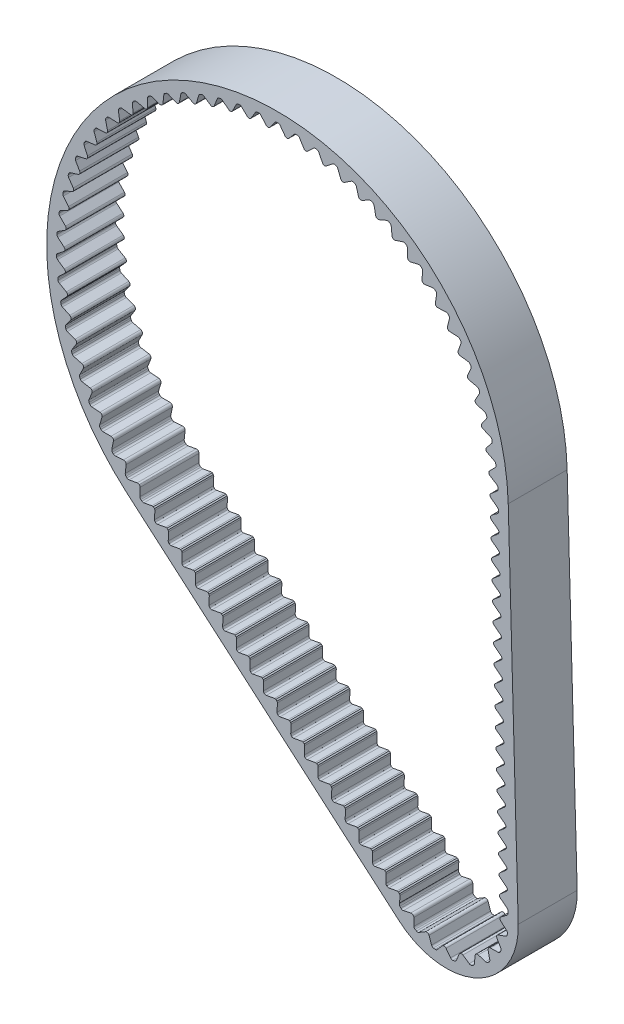
SolidWorks part; units mm, degrees
ref_plane "Face" through (0, 0, 0) normal (0, 0, 1) x (1, 0, 0)
ref_plane "Dessus" through (0, 0, 0) normal (0, 1, 0) x (1, 0, 0)
ref_plane "Droite" through (0, 0, 0) normal (1, 0, 0) x (0, 0, -1)
ref_plane "Plan1" through (0, 0, 6) normal (0, 0, 1) x (1, 0, 0)
sketch "Esquisse1" plane through (0, 0, 6) normal (0, 0, 1) x (1, 0, 0)
  line L0 (-15.3344, -17.8075) -> (12.3909, -41.6822)
  line L1 (24.5093, -35.9199) -> (23.4909, 0.6541)
  line L2 (22.6969, -34.5303) -> (23.3588, -35.04)
  line L3 (23.4562, -35.2422) -> (23.4441, -35.2419)
  line L4 (23.3776, -35.6789) -> (22.7552, -36.1447)
  line L5 (22.7403, -36.5329) -> (23.325, -37.0452)
  line L6 (23.2117, -37.6167) -> (22.4758, -37.8674)
  line L7 (22.3416, -38.2319) -> (22.7394, -38.8999)
  line L8 (22.4551, -39.4084) -> (21.6778, -39.4194)
  line L9 (21.4375, -39.7247) -> (21.6094, -40.4829)
  line L10 (21.1819, -40.8787) -> (20.4392, -40.6489)
  line L11 (20.1163, -40.865) -> (20.0455, -41.6392)
  line L12 (19.5166, -41.8835) -> (18.8812, -41.4354)
  line L13 (18.5074, -41.5412) -> (18.2008, -42.2556)
  line L14 (17.6223, -42.3245) -> (17.1565, -41.7021)
  line L15 (16.7683, -41.6871) -> (16.256, -42.2718)
  line L16 (15.6845, -42.1586) -> (15.4338, -41.4227)
  line L17 (15.0692, -41.2885) -> (14.4013, -41.6863)
  line L18 (13.8928, -41.402) -> (13.8818, -40.6246)
  line L19 (13.5765, -40.3843) -> (12.8183, -40.5562)
  line L20 (12.5335, -40.4331) -> (12.5299, -40.4377)
  line L21 (12.4225, -40.1287) -> (12.4389, -40.0758)
  line L22 (12.4389, -40.0758) -> (12.4571, -39.3994)
  line L23 (12.4207, -39.2626) -> (12.3042, -39.1623)
  line L24 (12.162, -39.1468) -> (11.3403, -39.2978)
  line L25 (11.1249, -39.2349) -> (11.1282, -39.2307)
  line L26 (11.0487, -39.0411) -> (11.0711, -38.2059)
  line L27 (11.0348, -38.0691) -> (10.9183, -37.9688)
  line L28 (10.776, -37.9533) -> (9.9543, -38.1043)
  line L29 (9.7389, -38.0415) -> (9.7422, -38.0372)
  line L30 (9.6627, -37.8476) -> (9.6851, -37.0124)
  line L31 (9.6488, -36.8757) -> (9.5323, -36.7754)
  line L32 (9.3901, -36.7599) -> (8.5684, -36.9108)
  line L33 (8.353, -36.848) -> (8.3563, -36.8437)
  line L34 (8.2768, -36.6541) -> (8.2992, -35.819)
  line L35 (8.2629, -35.6822) -> (8.1464, -35.5819)
  line L36 (8.0041, -35.5664) -> (7.1824, -35.7173)
  line L37 (6.967, -35.6545) -> (6.9703, -35.6503)
  line L38 (6.8908, -35.4607) -> (6.9132, -34.6255)
  line L39 (6.8769, -34.4887) -> (6.7604, -34.3884)
  line L40 (6.6182, -34.3729) -> (5.7965, -34.5239)
  line L41 (5.581, -34.4611) -> (5.5844, -34.4568)
  line L42 (5.5049, -34.2672) -> (5.5273, -33.432)
  line L43 (5.4909, -33.2953) -> (5.3745, -33.195)
  line L44 (5.2322, -33.1794) -> (4.4105, -33.3304)
  line L45 (4.1951, -33.2676) -> (4.1984, -33.2633)
  line L46 (4.1189, -33.0737) -> (4.1413, -32.2386)
  line L47 (4.105, -32.1018) -> (3.9885, -32.0015)
  line L48 (3.8462, -31.986) -> (3.0245, -32.1369)
  line L49 (2.8091, -32.0741) -> (2.8125, -32.0698)
  line L50 (2.733, -31.8802) -> (2.7554, -31.0451)
  line L51 (2.719, -30.9083) -> (2.6026, -30.808)
  line L52 (2.4603, -30.7925) -> (1.6386, -30.9435)
  line L53 (1.4232, -30.8807) -> (1.4265, -30.8764)
  line L54 (1.347, -30.6868) -> (1.3694, -29.8516)
  line L55 (1.3331, -29.7148) -> (1.2166, -29.6145)
  line L56 (1.0743, -29.599) -> (0.2526, -29.75)
  line L57 (0.0372, -29.6872) -> (0.0405, -29.6829)
  line L58 (-0.0389, -29.4933) -> (-0.0165, -28.6582)
  line L59 (-0.0529, -28.5214) -> (-0.1693, -28.4211)
  line L60 (-0.3116, -28.4056) -> (-1.1333, -28.5565)
  line L61 (-1.3487, -28.4937) -> (-1.3454, -28.4894)
  line L62 (-1.4249, -28.2998) -> (-1.4025, -27.4647)
  line L63 (-1.4388, -27.3279) -> (-1.5553, -27.2276)
  line L64 (-1.6976, -27.2121) -> (-2.5193, -27.363)
  line L65 (-2.7347, -27.3002) -> (-2.7314, -27.296)
  line L66 (-2.8108, -27.1064) -> (-2.7884, -26.2712)
  line L67 (-2.8248, -26.1344) -> (-2.9413, -26.0341)
  line L68 (-3.0835, -26.0186) -> (-3.9052, -26.1696)
  line L69 (-4.1206, -26.1068) -> (-4.1173, -26.1025)
  line L70 (-4.1968, -25.9129) -> (-4.1744, -25.0777)
  line L71 (-4.2107, -24.941) -> (-4.3272, -24.8407)
  line L72 (-4.4695, -24.8252) -> (-5.2912, -24.9761)
  line L73 (-5.5066, -24.9133) -> (-5.5033, -24.909)
  line L74 (-5.5827, -24.7194) -> (-5.5603, -23.8843)
  line L75 (-5.5967, -23.7475) -> (-5.7132, -23.6472)
  line L76 (-5.8554, -23.6317) -> (-6.6771, -23.7826)
  line L77 (-6.8925, -23.7198) -> (-6.8892, -23.7155)
  line L78 (-6.9687, -23.5259) -> (-6.9463, -22.6908)
  line L79 (-6.9826, -22.554) -> (-7.0991, -22.4537)
  line L80 (-7.2414, -22.4382) -> (-8.0631, -22.5892)
  line L81 (-8.2785, -22.5264) -> (-8.2752, -22.5221)
  line L82 (-8.3547, -22.3325) -> (-8.3323, -21.4973)
  line L83 (-8.3686, -21.3606) -> (-8.4851, -21.2602)
  line L84 (-8.6273, -21.2447) -> (-9.449, -21.3957)
  line L85 (-9.6644, -21.3329) -> (-9.6611, -21.3286)
  line L86 (-9.7406, -21.139) -> (-9.7182, -20.3039)
  line L87 (-9.7545, -20.1671) -> (-9.871, -20.0668)
  line L88 (-10.0133, -20.0513) -> (-10.835, -20.2022)
  line L89 (-11.0504, -20.1394) -> (-11.0471, -20.1351)
  line L90 (-11.1266, -19.9455) -> (-11.1042, -19.1104)
  line L91 (-11.1405, -18.9736) -> (-11.257, -18.8733)
  line L92 (-11.3992, -18.8578) -> (-12.2209, -19.0087)
  line L93 (-12.4364, -18.9459) -> (-12.433, -18.9417)
  line L94 (-12.5125, -18.7521) -> (-12.4901, -17.9169)
  line L95 (-12.5265, -17.7801) -> (-12.6429, -17.6798)
  line L96 (-12.7852, -17.6643) -> (-13.6069, -17.8153)
  line L97 (-14.0119, -17.4767) -> (-13.9895, -16.6416)
  line L98 (-14.0711, -16.45) -> (-14.0815, -16.441)
  line L99 (-14.2846, -16.389) -> (-15.1063, -16.54)
  line L100 (-15.5016, -16.17) -> (-15.4055, -15.3401)
  line L101 (-15.6771, -15.0624) -> (-16.5089, -15.1401)
  line L102 (-16.8701, -14.7367) -> (-16.701, -13.9185)
  line L103 (-16.947, -13.6179) -> (-17.7824, -13.6218)
  line L104 (-18.1065, -13.188) -> (-17.8658, -12.388)
  line L105 (-18.0842, -12.0668) -> (-18.9167, -11.9969)
  line L106 (-19.2012, -11.5362) -> (-18.8907, -10.7606)
  line L107 (-19.0799, -10.4213) -> (-19.903, -10.2781)
  line L108 (-20.1456, -9.794) -> (-19.7678, -9.0489)
  line L109 (-19.9263, -8.6943) -> (-20.7335, -8.4789)
  line L110 (-20.9324, -7.9752) -> (-20.4902, -7.2664)
  line L111 (-20.6167, -6.8992) -> (-21.4017, -6.6132)
  line L112 (-21.5553, -6.094) -> (-21.0522, -5.427)
  line L113 (-21.1458, -5.0501) -> (-21.9025, -4.6959)
  line L114 (-22.0096, -4.1651) -> (-21.4495, -3.5452)
  line L115 (-21.5094, -3.1614) -> (-22.2318, -2.7418)
  line L116 (-22.2916, -2.2036) -> (-21.6789, -1.6356)
  line L117 (-21.7046, -1.248) -> (-22.3871, -0.7662)
  line L118 (-22.3991, -0.2248) -> (-21.7386, 0.2868)
  line L119 (-21.73, 0.6751) -> (-22.3672, 1.2154)
  line L120 (-22.3313, 1.7557) -> (-21.6282, 2.2069)
  line L121 (-21.5853, 2.5929) -> (-22.1723, 3.1874)
  line L122 (-22.0887, 3.7225) -> (-21.3485, 4.1098)
  line L123 (-21.2717, 4.4905) -> (-21.8038, 5.1346)
  line L124 (-21.6733, 5.6601) -> (-20.9017, 5.9805)
  line L125 (-20.7915, 6.3529) -> (-21.2647, 7.0415)
  line L126 (-21.0883, 7.5534) -> (-20.2914, 7.8044)
  line L127 (-20.1487, 8.1656) -> (-20.5591, 8.8933)
  line L128 (-20.3382, 9.3877) -> (-19.5222, 9.5672)
  line L129 (-19.3482, 9.9144) -> (-19.6927, 10.6755)
  line L130 (-19.4289, 11.1484) -> (-18.6003, 11.2551)
  line L131 (-18.3962, 11.5856) -> (-18.6721, 12.3742)
  line L132 (-18.3676, 12.8219) -> (-17.5328, 12.855)
  line L133 (-17.3003, 13.1661) -> (-17.5054, 13.976)
  line L134 (-17.1625, 14.3951) -> (-16.328, 14.3542)
  line L135 (-16.069, 14.6436) -> (-16.2017, 15.4685)
  line L136 (-15.8231, 15.8556) -> (-14.9955, 15.7411)
  line L137 (-14.7119, 16.0065) -> (-14.7712, 16.8398)
  line L138 (-14.3599, 17.192) -> (-13.5456, 17.0048)
  line L139 (-13.2397, 17.2441) -> (-13.2251, 18.0794)
  line L140 (-12.7842, 18.3938) -> (-11.9897, 18.1354)
  line L141 (-11.6638, 18.3467) -> (-11.5755, 19.1775)
  line L142 (-11.1086, 19.4517) -> (-10.34, 19.1241)
  line L143 (-9.9967, 19.3058) -> (-9.8353, 20.1255)
  line L144 (-9.3459, 20.3574) -> (-8.6094, 19.9631)
  line L145 (-8.2513, 20.1138) -> (-8.0181, 20.916)
  line L146 (-7.5102, 21.1037) -> (-6.8113, 20.6459)
  line L147 (-6.4414, 20.7643) -> (-6.1382, 21.5428)
  line L148 (-5.6157, 21.6849) -> (-4.96, 21.1671)
  line L149 (-4.581, 21.2523) -> (-4.2102, 22.001)
  line L150 (-3.6772, 22.0963) -> (-3.0698, 21.5226)
  line L151 (-2.6848, 21.5741) -> (-2.2493, 22.287)
  line L152 (-1.7099, 22.3348) -> (-1.1556, 21.7097)
  line L153 (-0.7676, 21.7269) -> (-0.2707, 22.3986)
  line L154 (0.2707, 22.3986) -> (0.7676, 21.7269)
  line L155 (1.1556, 21.7097) -> (1.7099, 22.3348)
  line L156 (2.2493, 22.287) -> (2.6848, 21.5741)
  line L157 (3.0698, 21.5226) -> (3.6772, 22.0963)
  line L158 (4.2102, 22.001) -> (4.581, 21.2523)
  line L159 (4.96, 21.1671) -> (5.6157, 21.6849)
  line L160 (6.1382, 21.5428) -> (6.4414, 20.7643)
  line L161 (6.8113, 20.6459) -> (7.5102, 21.1037)
  line L162 (8.0181, 20.916) -> (8.2513, 20.1138)
  line L163 (8.6094, 19.9631) -> (9.3459, 20.3574)
  line L164 (9.8353, 20.1255) -> (9.9967, 19.3058)
  line L165 (10.34, 19.1241) -> (11.1086, 19.4517)
  line L166 (11.5755, 19.1775) -> (11.6638, 18.3467)
  line L167 (11.9897, 18.1354) -> (12.7842, 18.3938)
  line L168 (13.2251, 18.0794) -> (13.2397, 17.2441)
  line L169 (13.5456, 17.0048) -> (14.3599, 17.192)
  line L170 (14.7712, 16.8398) -> (14.7119, 16.0065)
  line L171 (14.9955, 15.7411) -> (15.8231, 15.8556)
  line L172 (16.2017, 15.4685) -> (16.069, 14.6436)
  line L173 (16.328, 14.3542) -> (17.1625, 14.3951)
  line L174 (17.5054, 13.976) -> (17.3003, 13.1661)
  line L175 (17.5328, 12.855) -> (18.3676, 12.8219)
  line L176 (18.6721, 12.3742) -> (18.3962, 11.5856)
  line L177 (18.6003, 11.2551) -> (19.4289, 11.1484)
  line L178 (19.6927, 10.6755) -> (19.3482, 9.9144)
  line L179 (19.5222, 9.5672) -> (20.3382, 9.3877)
  line L180 (20.5591, 8.8933) -> (20.1487, 8.1656)
  line L181 (20.2914, 7.8044) -> (21.0883, 7.5534)
  line L182 (21.2647, 7.0415) -> (20.7915, 6.3529)
  line L183 (20.9017, 5.9805) -> (21.6733, 5.6601)
  line L184 (21.8038, 5.1346) -> (21.2717, 4.4905)
  line L185 (21.3485, 4.1098) -> (22.0887, 3.7225)
  line L186 (22.1723, 3.1874) -> (21.5853, 2.5929)
  line L187 (21.6282, 2.2069) -> (22.3313, 1.7557)
  line L188 (22.3672, 1.2154) -> (21.73, 0.6751)
  line L189 (21.6417, 0.4908) -> (21.6425, 0.4641)
  line L190 (21.7386, 0.2868) -> (22.3991, -0.2248)
  line L191 (22.3871, -0.7662) -> (21.9854, -1.0498)
  line L192 (21.9854, -1.0498) -> (21.7709, -1.2327)
  line L193 (21.6931, -1.3529) -> (21.6974, -1.5065)
  line L194 (21.7805, -1.621) -> (22.4424, -2.1308)
  line L195 (22.5393, -2.3121) -> (22.5447, -2.3123)
  line L196 (22.4575, -2.519) -> (22.337, -2.6217)
  line L197 (22.2318, -2.7418) -> (22.1202, -2.8066)
  line L198 (22.1202, -2.8066) -> (21.8218, -3.061)
  line L199 (21.744, -3.1812) -> (21.7483, -3.3348)
  line L200 (21.8314, -3.4493) -> (22.4933, -3.9591)
  line L201 (22.5902, -4.1404) -> (22.5956, -4.1405)
  line L202 (22.5084, -4.3473) -> (21.8727, -4.8893)
  line L203 (21.7949, -5.0095) -> (21.7992, -5.1631)
  line L204 (21.8823, -5.2776) -> (22.5442, -5.7874)
  line L205 (22.6411, -5.9687) -> (22.6466, -5.9688)
  line L206 (22.5593, -6.1756) -> (21.9236, -6.7176)
  line L207 (21.8458, -6.8378) -> (21.8501, -6.9914)
  line L208 (21.9332, -7.1059) -> (22.5952, -7.6157)
  line L209 (22.6921, -7.797) -> (22.6975, -7.7971)
  line L210 (22.6102, -8.0038) -> (21.9745, -8.5459)
  line L211 (21.8967, -8.666) -> (21.901, -8.8197)
  line L212 (21.9842, -8.9342) -> (22.6461, -9.444)
  line L213 (22.743, -9.6253) -> (22.7484, -9.6254)
  line L214 (22.6611, -9.8321) -> (22.0254, -10.3742)
  line L215 (21.9476, -10.4943) -> (21.9519, -10.648)
  line L216 (22.0351, -10.7625) -> (22.697, -11.2723)
  line L217 (22.7939, -11.4536) -> (22.7993, -11.4537)
  line L218 (22.712, -11.6604) -> (22.0763, -12.2025)
  line L219 (21.9985, -12.3226) -> (22.0028, -12.4763)
  line L220 (22.086, -12.5908) -> (22.7479, -13.1005)
  line L221 (22.8448, -13.2819) -> (22.8502, -13.282)
  line L222 (22.7629, -13.4887) -> (22.1272, -14.0308)
  line L223 (22.0495, -14.1509) -> (22.0537, -14.3046)
  line L224 (22.1369, -14.4191) -> (22.7988, -14.9288)
  line L225 (22.8957, -15.1102) -> (22.9011, -15.1103)
  line L226 (22.8139, -15.317) -> (22.1781, -15.8591)
  line L227 (22.1004, -15.9792) -> (22.1046, -16.1329)
  line L228 (22.1878, -16.2474) -> (22.8497, -16.7571)
  line L229 (22.9466, -16.9385) -> (22.952, -16.9386)
  line L230 (22.8648, -17.1453) -> (22.229, -17.6874)
  line L231 (22.1513, -17.8075) -> (22.1556, -17.9612)
  line L232 (22.2387, -18.0757) -> (22.9006, -18.5854)
  line L233 (22.9975, -18.7667) -> (23.0029, -18.7669)
  line L234 (22.9157, -18.9736) -> (22.28, -19.5157)
  line L235 (22.2022, -19.6358) -> (22.2065, -19.7894)
  line L236 (22.2896, -19.904) -> (22.9515, -20.4137)
  line L237 (23.0484, -20.595) -> (23.0538, -20.5952)
  line L238 (22.9666, -20.8019) -> (22.3309, -21.3439)
  line L239 (22.2531, -21.4641) -> (22.2574, -21.6177)
  line L240 (22.3405, -21.7323) -> (23.0024, -22.242)
  line L241 (23.0993, -22.4233) -> (23.1047, -22.4235)
  line L242 (23.0175, -22.6302) -> (22.3818, -23.1722)
  line L243 (22.304, -23.2924) -> (22.3083, -23.446)
  line L244 (22.3914, -23.5605) -> (23.0533, -24.0703)
  line L245 (23.1502, -24.2516) -> (23.1557, -24.2517)
  line L246 (23.0684, -24.4585) -> (22.4327, -25.0005)
  line L247 (22.3549, -25.1207) -> (22.3592, -25.2743)
  line L248 (22.4423, -25.3888) -> (23.1043, -25.8986)
  line L249 (23.2012, -26.0799) -> (23.2066, -26.08)
  line L250 (23.1193, -26.2868) -> (22.4836, -26.8288)
  line L251 (22.4058, -26.949) -> (22.4101, -27.1026)
  line L252 (22.4933, -27.2171) -> (23.1552, -27.7269)
  line L253 (23.2521, -27.9082) -> (23.2575, -27.9083)
  line L254 (23.1702, -28.1151) -> (22.5345, -28.6571)
  line L255 (22.4567, -28.7773) -> (22.461, -28.9309)
  line L256 (22.5442, -29.0454) -> (23.2061, -29.5552)
  line L257 (23.303, -29.7365) -> (23.3084, -29.7366)
  line L258 (23.2211, -29.9433) -> (22.5854, -30.4854)
  line L259 (22.5076, -30.6055) -> (22.5119, -30.7592)
  line L260 (22.5951, -30.8737) -> (23.257, -31.3835)
  line L261 (23.3539, -31.5648) -> (23.3593, -31.5649)
  line L262 (23.272, -31.7716) -> (22.6363, -32.3137)
  line L263 (22.5586, -32.4338) -> (22.5628, -32.5875)
  line L264 (22.646, -32.702) -> (23.3079, -33.2118)
  line L265 (23.4048, -33.3931) -> (23.4102, -33.3932)
  line L266 (23.323, -33.5999) -> (22.6872, -34.142)
  line L267 (22.6802, -34.1482) -> (22.6193, -34.2346)
  line L268 (22.6095, -34.2621) -> (22.6137, -34.4158)
  line L269 (0, 0) -> (17.1772, -36.124) construction
  line L270 (0, -52.5) -> (0, 52.5) construction
  arc A0 (12.3909, -41.6822) -> (24.5093, -35.9199) centre (17.1772, -36.124) ccw
  arc A1 (23.4909, 0.6541) -> (-15.3344, -17.8075) centre (0, 0) ccw
  arc A2 (23.3588, -35.04) -> (23.4562, -35.2422) centre (23.2063, -35.2381) cw
  arc A3 (23.4441, -35.2419) -> (23.458, -35.2975) centre (23.2101, -35.3301) cw
  arc A4 (23.458, -35.2975) -> (23.4764, -35.4522) centre (17.1772, -36.124) cw
  arc A5 (23.4764, -35.4522) -> (23.3776, -35.6789) centre (23.2278, -35.4787) cw
  arc A6 (22.7552, -36.1447) -> (22.7403, -36.5329) centre (22.905, -36.3448) ccw
  arc A7 (23.325, -37.0452) -> (23.406, -37.2788) centre (23.1602, -37.2332) cw
  arc A8 (23.406, -37.2788) -> (23.3757, -37.4317) centre (17.1772, -36.124) cw
  arc A9 (23.3757, -37.4317) -> (23.2117, -37.6167) centre (23.1311, -37.3801) cw
  arc A10 (22.4758, -37.8674) -> (22.3416, -38.2319) centre (22.5564, -38.104) ccw
  arc A11 (22.7394, -38.8999) -> (22.7443, -39.1471) centre (22.5246, -39.0278) cw
  arc A12 (22.7443, -39.1471) -> (22.6683, -39.2831) centre (17.1772, -36.124) cw
  arc A13 (22.6683, -39.2831) -> (22.4551, -39.4084) centre (22.4516, -39.1585) cw
  arc A14 (21.6778, -39.4194) -> (21.4375, -39.7247) centre (21.6813, -39.6694) ccw
  arc A15 (21.6094, -40.4829) -> (21.5377, -40.7195) centre (21.3656, -40.5381) cw
  arc A16 (21.5377, -40.7195) -> (21.4233, -40.8254) centre (17.1772, -36.124) cw
  arc A17 (21.4233, -40.8254) -> (21.1819, -40.8787) centre (21.2557, -40.6398) cw
  arc A18 (20.4392, -40.6489) -> (20.1163, -40.865) centre (20.3653, -40.8877) ccw
  arc A19 (20.0455, -41.6392) -> (19.9042, -41.842) centre (19.7965, -41.6164) cw
  arc A20 (19.9042, -41.842) -> (19.7627, -41.9074) centre (17.1772, -36.124) cw
  arc A21 (19.7627, -41.9074) -> (19.5166, -41.8835) centre (19.6607, -41.6792) cw
  arc A22 (18.8812, -41.4354) -> (18.5074, -41.5412) centre (18.7372, -41.6398) ccw
  arc A23 (18.2008, -42.2556) -> (18.0037, -42.4049) centre (17.9711, -42.157) cw
  arc A24 (18.0037, -42.4049) -> (17.849, -42.4233) centre (17.1772, -36.124) cw
  arc A25 (17.849, -42.4233) -> (17.6223, -42.3245) centre (17.8225, -42.1747) cw
  arc A26 (17.1565, -41.7021) -> (16.7683, -41.6871) centre (16.9564, -41.8519) ccw
  arc A27 (16.256, -42.2718) -> (16.0224, -42.3529) centre (16.068, -42.1071) cw
  arc A28 (16.0224, -42.3529) -> (15.8695, -42.3226) centre (17.1772, -36.124) cw
  arc A29 (15.8695, -42.3226) -> (15.6845, -42.1586) centre (15.9211, -42.078) cw
  arc A30 (15.4338, -41.4227) -> (15.0692, -41.2885) centre (15.1972, -41.5033) ccw
  arc A31 (14.4013, -41.6863) -> (14.1541, -41.6912) centre (14.2734, -41.4715) cw
  arc A32 (14.1541, -41.6912) -> (14.0181, -41.6151) centre (17.1772, -36.124) cw
  arc A33 (14.0181, -41.6151) -> (13.8928, -41.402) centre (14.1427, -41.3984) cw
  arc A34 (13.8818, -40.6246) -> (13.5765, -40.3843) centre (13.6318, -40.6282) ccw
  arc A35 (12.8183, -40.5562) -> (12.5817, -40.4845) centre (12.763, -40.3124) cw
  arc A36 (12.5817, -40.4845) -> (12.5335, -40.4331) centre (17.1772, -36.124) cw
  arc A37 (12.5299, -40.4377) -> (12.4595, -40.3501) centre (12.6846, -40.2412) cw
  arc A38 (12.4595, -40.3501) -> (12.4225, -40.1287) centre (12.6614, -40.2026) cw
  arc A39 (12.4571, -39.3994) -> (12.4207, -39.2626) centre (12.2071, -39.3926) ccw
  arc A40 (12.3042, -39.1623) -> (12.162, -39.1468) centre (12.2071, -39.3927) ccw
  arc A41 (11.3403, -39.2978) -> (11.1249, -39.2349) centre (11.2951, -39.0519) cw
  arc A42 (11.1282, -39.2307) -> (11.0487, -39.0411) centre (11.2986, -39.0478) cw
  arc A43 (11.0711, -38.2059) -> (11.0348, -38.0691) centre (10.8212, -38.1991) ccw
  arc A44 (10.9183, -37.9688) -> (10.776, -37.9533) centre (10.8212, -38.1992) ccw
  arc A45 (9.9543, -38.1043) -> (9.7389, -38.0415) centre (9.9091, -37.8584) cw
  arc A46 (9.7422, -38.0372) -> (9.6627, -37.8476) centre (9.9127, -37.8543) cw
  arc A47 (9.6851, -37.0124) -> (9.6488, -36.8757) centre (9.4352, -37.0056) ccw
  arc A48 (9.5323, -36.7754) -> (9.3901, -36.7599) centre (9.4352, -37.0057) ccw
  arc A49 (8.5684, -36.9108) -> (8.353, -36.848) centre (8.5232, -36.6649) cw
  arc A50 (8.3563, -36.8437) -> (8.2768, -36.6541) centre (8.5267, -36.6608) cw
  arc A51 (8.2992, -35.819) -> (8.2629, -35.6822) centre (8.0493, -35.8122) ccw
  arc A52 (8.1464, -35.5819) -> (8.0041, -35.5664) centre (8.0493, -35.8123) ccw
  arc A53 (7.1824, -35.7173) -> (6.967, -35.6545) centre (7.1372, -35.4715) cw
  arc A54 (6.9703, -35.6503) -> (6.8908, -35.4607) centre (7.1407, -35.4674) cw
  arc A55 (6.9132, -34.6255) -> (6.8769, -34.4887) centre (6.6633, -34.6187) ccw
  arc A56 (6.7604, -34.3884) -> (6.6182, -34.3729) centre (6.6633, -34.6188) ccw
  arc A57 (5.7965, -34.5239) -> (5.581, -34.4611) centre (5.7513, -34.278) cw
  arc A58 (5.5844, -34.4568) -> (5.5049, -34.2672) centre (5.7548, -34.2739) cw
  arc A59 (5.5273, -33.432) -> (5.4909, -33.2953) centre (5.2774, -33.4252) ccw
  arc A60 (5.3745, -33.195) -> (5.2322, -33.1794) centre (5.2774, -33.4253) ccw
  arc A61 (4.4105, -33.3304) -> (4.1951, -33.2676) centre (4.3653, -33.0845) cw
  arc A62 (4.1984, -33.2633) -> (4.1189, -33.0737) centre (4.3688, -33.0804) cw
  arc A63 (4.1413, -32.2386) -> (4.105, -32.1018) centre (3.8914, -32.2317) ccw
  arc A64 (3.9885, -32.0015) -> (3.8462, -31.986) centre (3.8914, -32.2319) ccw
  arc A65 (3.0245, -32.1369) -> (2.8091, -32.0741) centre (2.9794, -31.891) cw
  arc A66 (2.8125, -32.0698) -> (2.733, -31.8802) centre (2.9829, -31.8869) cw
  arc A67 (2.7554, -31.0451) -> (2.719, -30.9083) centre (2.5055, -31.0383) ccw
  arc A68 (2.6026, -30.808) -> (2.4603, -30.7925) centre (2.5055, -31.0384) ccw
  arc A69 (1.6386, -30.9435) -> (1.4232, -30.8807) centre (1.5934, -30.6976) cw
  arc A70 (1.4265, -30.8764) -> (1.347, -30.6868) centre (1.5969, -30.6935) cw
  arc A71 (1.3694, -29.8516) -> (1.3331, -29.7148) centre (1.1195, -29.8448) ccw
  arc A72 (1.2166, -29.6145) -> (1.0743, -29.599) centre (1.1195, -29.8449) ccw
  arc A73 (0.2526, -29.75) -> (0.0372, -29.6872) centre (0.2075, -29.5041) cw
  arc A74 (0.0405, -29.6829) -> (-0.0389, -29.4933) centre (0.211, -29.5) cw
  arc A75 (-0.0165, -28.6582) -> (-0.0529, -28.5214) centre (-0.2664, -28.6513) ccw
  arc A76 (-0.1693, -28.4211) -> (-0.3116, -28.4056) centre (-0.2664, -28.6514) ccw
  arc A77 (-1.1333, -28.5565) -> (-1.3487, -28.4937) centre (-1.1785, -28.3106) cw
  arc A78 (-1.3454, -28.4894) -> (-1.4249, -28.2998) centre (-1.175, -28.3065) cw
  arc A79 (-1.4025, -27.4647) -> (-1.4388, -27.3279) centre (-1.6524, -27.4579) ccw
  arc A80 (-1.5553, -27.2276) -> (-1.6976, -27.2121) centre (-1.6524, -27.458) ccw
  arc A81 (-2.5193, -27.363) -> (-2.7347, -27.3002) centre (-2.5644, -27.1172) cw
  arc A82 (-2.7314, -27.296) -> (-2.8108, -27.1064) centre (-2.5609, -27.1131) cw
  arc A83 (-2.7884, -26.2712) -> (-2.8248, -26.1344) centre (-3.0383, -26.2644) ccw
  arc A84 (-2.9413, -26.0341) -> (-3.0835, -26.0186) centre (-3.0384, -26.2645) ccw
  arc A85 (-3.9052, -26.1696) -> (-4.1206, -26.1068) centre (-3.9504, -25.9237) cw
  arc A86 (-4.1173, -26.1025) -> (-4.1968, -25.9129) centre (-3.9469, -25.9196) cw
  arc A87 (-4.1744, -25.0777) -> (-4.2107, -24.941) centre (-4.4243, -25.0709) ccw
  arc A88 (-4.3272, -24.8407) -> (-4.4695, -24.8252) centre (-4.4243, -25.071) ccw
  arc A89 (-5.2912, -24.9761) -> (-5.5066, -24.9133) centre (-5.3363, -24.7302) cw
  arc A90 (-5.5033, -24.909) -> (-5.5827, -24.7194) centre (-5.3328, -24.7261) cw
  arc A91 (-5.5603, -23.8843) -> (-5.5967, -23.7475) centre (-5.8103, -23.8774) ccw
  arc A92 (-5.7132, -23.6472) -> (-5.8554, -23.6317) centre (-5.8103, -23.8776) ccw
  arc A93 (-6.6771, -23.7826) -> (-6.8925, -23.7198) centre (-6.7223, -23.5367) cw
  arc A94 (-6.8892, -23.7155) -> (-6.9687, -23.5259) centre (-6.7188, -23.5326) cw
  arc A95 (-6.9463, -22.6908) -> (-6.9826, -22.554) centre (-7.1962, -22.684) ccw
  arc A96 (-7.0991, -22.4537) -> (-7.2414, -22.4382) centre (-7.1962, -22.6841) ccw
  arc A97 (-8.0631, -22.5892) -> (-8.2785, -22.5264) centre (-8.1083, -22.3433) cw
  arc A98 (-8.2752, -22.5221) -> (-8.3547, -22.3325) centre (-8.1047, -22.3392) cw
  arc A99 (-8.3323, -21.4973) -> (-8.3686, -21.3606) centre (-8.5822, -21.4905) ccw
  arc A100 (-8.4851, -21.2602) -> (-8.6273, -21.2447) centre (-8.5822, -21.4906) ccw
  arc A101 (-9.449, -21.3957) -> (-9.6644, -21.3329) centre (-9.4942, -21.1498) cw
  arc A102 (-9.6611, -21.3286) -> (-9.7406, -21.139) centre (-9.4907, -21.1457) cw
  arc A103 (-9.7182, -20.3039) -> (-9.7545, -20.1671) centre (-9.9681, -20.297) ccw
  arc A104 (-9.871, -20.0668) -> (-10.0133, -20.0513) centre (-9.9681, -20.2972) ccw
  arc A105 (-10.835, -20.2022) -> (-11.0504, -20.1394) centre (-10.8802, -19.9563) cw
  arc A106 (-11.0471, -20.1351) -> (-11.1266, -19.9455) centre (-10.8767, -19.9522) cw
  arc A107 (-11.1042, -19.1104) -> (-11.1405, -18.9736) centre (-11.3541, -19.1036) ccw
  arc A108 (-11.257, -18.8733) -> (-11.3992, -18.8578) centre (-11.3541, -19.1037) ccw
  arc A109 (-12.2209, -19.0087) -> (-12.4364, -18.9459) centre (-12.2661, -18.7629) cw
  arc A110 (-12.433, -18.9417) -> (-12.5125, -18.7521) centre (-12.2626, -18.7588) cw
  arc A111 (-12.4901, -17.9169) -> (-12.5265, -17.7801) centre (-12.74, -17.9101) ccw
  arc A112 (-12.6429, -17.6798) -> (-12.7852, -17.6643) centre (-12.74, -17.9102) ccw
  arc A113 (-13.6069, -17.8153) -> (-13.8055, -17.7668) centre (-13.6521, -17.5694) cw
  arc A114 (-13.8055, -17.7668) -> (-13.9166, -17.6799) centre (0, 0) cw
  arc A115 (-13.9166, -17.6799) -> (-14.0119, -17.4767) centre (-13.762, -17.4834) cw
  arc A116 (-13.9895, -16.6416) -> (-14.0711, -16.45) centre (-14.2394, -16.6349) ccw
  arc A117 (-14.0815, -16.441) -> (-14.2846, -16.389) centre (-14.2394, -16.6349) ccw
  arc A118 (-15.1063, -16.54) -> (-15.3217, -16.4771) centre (-15.1514, -16.2941) cw
  arc A119 (-15.3217, -16.4771) -> (-15.4247, -16.3807) centre (0, 0) cw
  arc A120 (-15.4247, -16.3807) -> (-15.5016, -16.17) centre (-15.2533, -16.1987) cw
  arc A121 (-15.4055, -15.3401) -> (-15.6771, -15.0624) centre (-15.6539, -15.3113) ccw
  arc A122 (-16.5089, -15.1401) -> (-16.718, -15.0585) centre (-16.5322, -14.8912) cw
  arc A123 (-16.718, -15.0585) -> (-16.8121, -14.9534) centre (0, 0) cw
  arc A124 (-16.8121, -14.9534) -> (-16.8701, -14.7367) centre (-16.6253, -14.7873) cw
  arc A125 (-16.701, -13.9185) -> (-16.947, -13.6179) centre (-16.9458, -13.8679) ccw
  arc A126 (-17.7824, -13.6218) -> (-17.9834, -13.5221) centre (-17.7836, -13.3718) cw
  arc A127 (-17.9834, -13.5221) -> (-18.0679, -13.409) centre (0, 0) cw
  arc A128 (-18.0679, -13.409) -> (-18.1065, -13.188) centre (-17.8671, -13.2601) cw
  arc A129 (-17.8658, -12.388) -> (-18.0842, -12.0668) centre (-18.1052, -12.316) ccw
  arc A130 (-18.9167, -11.9969) -> (-19.1081, -11.8798) centre (-18.8958, -11.7478) cw
  arc A131 (-19.1081, -11.8798) -> (-19.1822, -11.7597) centre (0, 0) cw
  arc A132 (-19.1822, -11.7597) -> (-19.2012, -11.5362) centre (-18.9691, -11.6291) cw
  arc A133 (-18.8907, -10.7606) -> (-19.0799, -10.4213) centre (-19.1228, -10.6676) ccw
  arc A134 (-19.903, -10.2781) -> (-20.0833, -10.1445) centre (-19.8601, -10.0318) cw
  arc A135 (-20.0833, -10.1445) -> (-20.1465, -10.0184) centre (0, 0) cw
  arc A136 (-20.1465, -10.0184) -> (-20.1456, -9.794) centre (-19.9227, -9.9071) cw
  arc A137 (-19.7678, -9.0489) -> (-19.9263, -8.6943) centre (-19.9908, -8.9358) ccw
  arc A138 (-20.7335, -8.4789) -> (-20.9013, -8.3299) centre (-20.669, -8.2373) cw
  arc A139 (-20.9013, -8.3299) -> (-20.9531, -8.1986) centre (0, 0) cw
  arc A140 (-20.9531, -8.1986) -> (-20.9324, -7.9752) centre (-20.7203, -8.1075) cw
  arc A141 (-20.4902, -7.2664) -> (-20.6167, -6.8992) centre (-20.7023, -7.1341) ccw
  arc A142 (-21.4017, -6.6132) -> (-21.5557, -6.45) centre (-21.3162, -6.3783) cw
  arc A143 (-21.5557, -6.45) -> (-21.5957, -6.3147) centre (0, 0) cw
  arc A144 (-21.5957, -6.3147) -> (-21.5553, -6.094) centre (-21.3558, -6.2445) cw
  arc A145 (-21.0522, -5.427) -> (-21.1458, -5.0501) centre (-21.2518, -5.2765) ccw
  arc A146 (-21.9025, -4.6959) -> (-22.0414, -4.5197) centre (-21.7965, -4.4695) cw
  arc A147 (-22.0414, -4.5197) -> (-22.0693, -4.3814) centre (0, 0) cw
  arc A148 (-22.0693, -4.3814) -> (-22.0096, -4.1651) centre (-21.8241, -4.3327) cw
  arc A149 (-21.4495, -3.5452) -> (-21.5094, -3.1614) centre (-21.635, -3.3776) ccw
  arc A150 (-22.2318, -2.7418) -> (-22.3546, -2.554) centre (-22.1062, -2.5256) cw
  arc A151 (-22.3546, -2.554) -> (-22.3702, -2.4137) centre (0, 0) cw
  arc A152 (-22.3702, -2.4137) -> (-22.2916, -2.2036) centre (-22.1216, -2.3869) cw
  arc A153 (-21.6789, -1.6356) -> (-21.7046, -1.248) centre (-21.8488, -1.4523) ccw
  arc A154 (-22.3871, -0.7662) -> (-22.4928, -0.5683) centre (-22.2429, -0.562) cw
  arc A155 (-22.4928, -0.5683) -> (-22.4959, -0.4272) centre (0, 0) cw
  arc A156 (-22.4959, -0.4272) -> (-22.3991, -0.2248) centre (-22.246, -0.4225) cw
  arc A157 (-21.7386, 0.2868) -> (-21.73, 0.6751) centre (-21.8917, 0.4844) ccw
  arc A158 (-22.3672, 1.2154) -> (-22.455, 1.4219) centre (-22.2055, 1.4061) cw
  arc A159 (-22.455, 1.4219) -> (-22.4457, 1.5626) centre (0, 0) cw
  arc A160 (-22.4457, 1.5626) -> (-22.3313, 1.7557) centre (-22.1963, 1.5453) cw
  arc A161 (-21.6282, 2.2069) -> (-21.5853, 2.5929) centre (-21.7632, 2.4173) ccw
  arc A162 (-22.1723, 3.1874) -> (-22.2415, 3.4009) centre (-21.9944, 3.3631) cw
  arc A163 (-22.2415, 3.4009) -> (-22.2197, 3.5403) centre (0, 0) cw
  arc A164 (-22.2197, 3.5403) -> (-22.0887, 3.7225) centre (-21.9728, 3.5009) cw
  arc A165 (-21.3485, 4.1098) -> (-21.2717, 4.4905) centre (-21.4644, 4.3313) ccw
  arc A166 (-21.8038, 5.1346) -> (-21.8539, 5.3533) centre (-21.6111, 5.2938) cw
  arc A167 (-21.8539, 5.3533) -> (-21.8199, 5.4902) centre (0, 0) cw
  arc A168 (-21.8199, 5.4902) -> (-21.6733, 5.6601) centre (-21.5774, 5.4292) cw
  arc A169 (-20.9017, 5.9805) -> (-20.7915, 6.3529) centre (-20.9976, 6.2113) ccw
  arc A170 (-21.2647, 7.0415) -> (-21.2952, 7.2638) centre (-21.0586, 7.1831) cw
  arc A171 (-21.2952, 7.2638) -> (-21.2493, 7.3972) centre (0, 0) cw
  arc A172 (-21.2493, 7.3972) -> (-21.0883, 7.5534) centre (-21.0132, 7.315) cw
  arc A173 (-20.2914, 7.8044) -> (-20.1487, 8.1656) centre (-20.3665, 8.0428) ccw
  arc A174 (-20.5591, 8.8933) -> (-20.5699, 9.1174) centre (-20.3414, 9.0161) cw
  arc A175 (-20.5699, 9.1174) -> (-20.5124, 9.2462) centre (0, 0) cw
  arc A176 (-20.5124, 9.2462) -> (-20.3382, 9.3877) centre (-20.2844, 9.1435) cw
  arc A177 (-19.5222, 9.5672) -> (-19.3482, 9.9144) centre (-19.5759, 9.8113) ccw
  arc A178 (-19.6927, 10.6755) -> (-19.6836, 10.8997) centre (-19.4649, 10.7786) cw
  arc A179 (-19.6836, 10.8997) -> (-19.6149, 11.0229) centre (0, 0) cw
  arc A180 (-19.6149, 11.0229) -> (-19.4289, 11.1484) centre (-19.397, 10.9005) cw
  arc A181 (-18.6003, 11.2551) -> (-18.3962, 11.5856) centre (-18.6322, 11.5031) ccw
  arc A182 (-18.6721, 12.3742) -> (-18.6433, 12.5967) centre (-18.4362, 12.4568) cw
  arc A183 (-18.6433, 12.5967) -> (-18.5639, 12.7134) centre (0, 0) cw
  arc A184 (-18.5639, 12.7134) -> (-18.3676, 12.8219) centre (-18.3577, 12.5721) cw
  arc A185 (-17.5328, 12.855) -> (-17.3003, 13.1661) centre (-17.5427, 13.1048) ccw
  arc A186 (-17.5054, 13.976) -> (-17.457, 14.1951) centre (-17.2631, 14.0374) cw
  arc A187 (-17.457, 14.1951) -> (-17.3677, 14.3043) centre (0, 0) cw
  arc A188 (-17.3677, 14.3043) -> (-17.1625, 14.3951) centre (-17.1747, 14.1454) cw
  arc A189 (-16.328, 14.3542) -> (-16.069, 14.6436) centre (-16.3158, 14.6039) ccw
  arc A190 (-16.2017, 15.4685) -> (-16.1342, 15.6824) centre (-15.9549, 15.5082) cw
  arc A191 (-16.1342, 15.6824) -> (-16.0355, 15.7833) centre (0, 0) cw
  arc A192 (-16.0355, 15.7833) -> (-15.8231, 15.8556) centre (-15.8573, 15.6079) cw
  arc A193 (-14.9955, 15.7411) -> (-14.7119, 16.0065) centre (-14.9613, 15.9887) ccw
  arc A194 (-14.7712, 16.8398) -> (-14.685, 17.047) centre (-14.5219, 16.8576) cw
  arc A195 (-14.685, 17.047) -> (-14.5778, 17.1387) centre (0, 0) cw
  arc A196 (-14.5778, 17.1387) -> (-14.3599, 17.192) centre (-14.4159, 16.9483) cw
  arc A197 (-13.5456, 17.0048) -> (-13.2397, 17.2441) centre (-13.4896, 17.2485) ccw
  arc A198 (-13.2251, 18.0794) -> (-13.1209, 18.2782) centre (-12.9751, 18.0751) cw
  arc A199 (-13.1209, 18.2782) -> (-13.0061, 18.3601) centre (0, 0) cw
  arc A200 (-13.0061, 18.3601) -> (-12.7842, 18.3938) centre (-12.8616, 18.1561) cw
  arc A201 (-11.9897, 18.1354) -> (-11.6638, 18.3467) centre (-11.9124, 18.3732) ccw
  arc A202 (-11.5755, 19.1775) -> (-11.4542, 19.3663) centre (-11.3269, 19.1511) cw
  arc A203 (-11.4542, 19.3663) -> (-11.3325, 19.4377) centre (0, 0) cw
  arc A204 (-11.3325, 19.4377) -> (-11.1086, 19.4517) centre (-11.2066, 19.2217) cw
  arc A205 (-10.34, 19.1241) -> (-9.9967, 19.3058) centre (-10.242, 19.3541) ccw
  arc A206 (-9.8353, 20.1255) -> (-9.6978, 20.3028) centre (-9.59, 20.0772) cw
  arc A207 (-9.6978, 20.3028) -> (-9.5703, 20.3632) centre (0, 0) cw
  arc A208 (-9.5703, 20.3632) -> (-9.3459, 20.3574) centre (-9.4639, 20.137) cw
  arc A209 (-8.6094, 19.9631) -> (-8.2513, 20.1138) centre (-8.4914, 20.1836) ccw
  arc A210 (-8.0181, 20.916) -> (-7.8654, 21.0804) centre (-7.778, 20.8462) cw
  arc A211 (-7.8654, 21.0804) -> (-7.7331, 21.1293) centre (0, 0) cw
  arc A212 (-7.7331, 21.1293) -> (-7.5102, 21.1037) centre (-7.6472, 20.8946) cw
  arc A213 (-6.8113, 20.6459) -> (-6.4414, 20.7643) centre (-6.6743, 20.855) ccw
  arc A214 (-6.1382, 21.5428) -> (-5.9716, 21.6931) centre (-5.9052, 21.4521) cw
  arc A215 (-5.9716, 21.6931) -> (-5.8354, 21.7301) centre (0, 0) cw
  arc A216 (-5.8354, 21.7301) -> (-5.6157, 21.6849) centre (-5.7706, 21.4887) cw
  arc A217 (-4.96, 21.1671) -> (-4.581, 21.2523) centre (-4.8051, 21.3633) ccw
  arc A218 (-4.2102, 22.001) -> (-4.031, 22.136) centre (-3.9862, 21.89) cw
  arc A219 (-4.031, 22.136) -> (-3.8921, 22.1608) centre (0, 0) cw
  arc A220 (-3.8921, 22.1608) -> (-3.6772, 22.0963) centre (-3.8488, 21.9146) cw
  arc A221 (-3.0698, 21.5226) -> (-2.6848, 21.5741) centre (-2.8982, 21.7044) ccw
  arc A222 (-2.2493, 22.287) -> (-2.0588, 22.4056) centre (-2.0359, 22.1567) cw
  arc A223 (-2.0588, 22.4056) -> (-1.9183, 22.4181) centre (0, 0) cw
  arc A224 (-1.9183, 22.4181) -> (-1.7099, 22.3348) centre (-1.897, 22.169) cw
  arc A225 (-1.1556, 21.7097) -> (-0.7676, 21.7269) centre (-0.9686, 21.8756) ccw
  arc A226 (-0.2707, 22.3986) -> (-0.0705, 22.4999) centre (-0.0698, 22.2499) cw
  arc A227 (-0.0705, 22.4999) -> (0.0705, 22.4999) centre (0, 0) cw
  arc A228 (0.0705, 22.4999) -> (0.2707, 22.3986) centre (0.0698, 22.2499) cw
  arc A229 (0.7676, 21.7269) -> (1.1556, 21.7097) centre (0.9686, 21.8756) ccw
  arc A230 (1.7099, 22.3348) -> (1.9183, 22.4181) centre (1.897, 22.169) cw
  arc A231 (1.9183, 22.4181) -> (2.0588, 22.4056) centre (0, 0) cw
  arc A232 (2.0588, 22.4056) -> (2.2493, 22.287) centre (2.0359, 22.1567) cw
  arc A233 (2.6848, 21.5741) -> (3.0698, 21.5226) centre (2.8982, 21.7044) ccw
  arc A234 (3.6772, 22.0963) -> (3.8921, 22.1608) centre (3.8488, 21.9146) cw
  arc A235 (3.8921, 22.1608) -> (4.031, 22.136) centre (0, 0) cw
  arc A236 (4.031, 22.136) -> (4.2102, 22.001) centre (3.9862, 21.89) cw
  arc A237 (4.581, 21.2523) -> (4.96, 21.1671) centre (4.8051, 21.3633) ccw
  arc A238 (5.6157, 21.6849) -> (5.8354, 21.7301) centre (5.7706, 21.4887) cw
  arc A239 (5.8354, 21.7301) -> (5.9716, 21.6931) centre (0, 0) cw
  arc A240 (5.9716, 21.6931) -> (6.1382, 21.5428) centre (5.9052, 21.4521) cw
  arc A241 (6.4414, 20.7643) -> (6.8113, 20.6459) centre (6.6743, 20.855) ccw
  arc A242 (7.5102, 21.1037) -> (7.7331, 21.1293) centre (7.6472, 20.8946) cw
  arc A243 (7.7331, 21.1293) -> (7.8654, 21.0804) centre (0, 0) cw
  arc A244 (7.8654, 21.0804) -> (8.0181, 20.916) centre (7.778, 20.8462) cw
  arc A245 (8.2513, 20.1138) -> (8.6094, 19.9631) centre (8.4914, 20.1836) ccw
  arc A246 (9.3459, 20.3574) -> (9.5703, 20.3632) centre (9.4639, 20.137) cw
  arc A247 (9.5703, 20.3632) -> (9.6978, 20.3028) centre (0, 0) cw
  arc A248 (9.6978, 20.3028) -> (9.8353, 20.1255) centre (9.59, 20.0772) cw
  arc A249 (9.9967, 19.3058) -> (10.34, 19.1241) centre (10.242, 19.3541) ccw
  arc A250 (11.1086, 19.4517) -> (11.3325, 19.4377) centre (11.2066, 19.2217) cw
  arc A251 (11.3325, 19.4377) -> (11.4542, 19.3663) centre (0, 0) cw
  arc A252 (11.4542, 19.3663) -> (11.5755, 19.1775) centre (11.3269, 19.1511) cw
  arc A253 (11.6638, 18.3467) -> (11.9897, 18.1354) centre (11.9124, 18.3732) ccw
  arc A254 (12.7842, 18.3938) -> (13.0061, 18.3601) centre (12.8616, 18.1561) cw
  arc A255 (13.0061, 18.3601) -> (13.1209, 18.2782) centre (0, 0) cw
  arc A256 (13.1209, 18.2782) -> (13.2251, 18.0794) centre (12.9751, 18.0751) cw
  arc A257 (13.2397, 17.2441) -> (13.5456, 17.0048) centre (13.4896, 17.2485) ccw
  arc A258 (14.3599, 17.192) -> (14.5778, 17.1387) centre (14.4159, 16.9483) cw
  arc A259 (14.5778, 17.1387) -> (14.685, 17.047) centre (0, 0) cw
  arc A260 (14.685, 17.047) -> (14.7712, 16.8398) centre (14.5219, 16.8576) cw
  arc A261 (14.7119, 16.0065) -> (14.9955, 15.7411) centre (14.9613, 15.9887) ccw
  arc A262 (15.8231, 15.8556) -> (16.0355, 15.7833) centre (15.8573, 15.6079) cw
  arc A263 (16.0355, 15.7833) -> (16.1342, 15.6824) centre (0, 0) cw
  arc A264 (16.1342, 15.6824) -> (16.2017, 15.4685) centre (15.9549, 15.5082) cw
  arc A265 (16.069, 14.6436) -> (16.328, 14.3542) centre (16.3158, 14.6039) ccw
  arc A266 (17.1625, 14.3951) -> (17.3677, 14.3043) centre (17.1747, 14.1454) cw
  arc A267 (17.3677, 14.3043) -> (17.457, 14.1951) centre (0, 0) cw
  arc A268 (17.457, 14.1951) -> (17.5054, 13.976) centre (17.2631, 14.0374) cw
  arc A269 (17.3003, 13.1661) -> (17.5328, 12.855) centre (17.5427, 13.1048) ccw
  arc A270 (18.3676, 12.8219) -> (18.5639, 12.7134) centre (18.3577, 12.5721) cw
  arc A271 (18.5639, 12.7134) -> (18.6433, 12.5967) centre (0, 0) cw
  arc A272 (18.6433, 12.5967) -> (18.6721, 12.3742) centre (18.4362, 12.4568) cw
  arc A273 (18.3962, 11.5856) -> (18.6003, 11.2551) centre (18.6322, 11.5031) ccw
  arc A274 (19.4289, 11.1484) -> (19.6149, 11.0229) centre (19.397, 10.9005) cw
  arc A275 (19.6149, 11.0229) -> (19.6836, 10.8997) centre (0, 0) cw
  arc A276 (19.6836, 10.8997) -> (19.6927, 10.6755) centre (19.4649, 10.7786) cw
  arc A277 (19.3482, 9.9144) -> (19.5222, 9.5672) centre (19.5759, 9.8113) ccw
  arc A278 (20.3382, 9.3877) -> (20.5124, 9.2462) centre (20.2844, 9.1435) cw
  arc A279 (20.5124, 9.2462) -> (20.5699, 9.1174) centre (0, 0) cw
  arc A280 (20.5699, 9.1174) -> (20.5591, 8.8933) centre (20.3414, 9.0161) cw
  arc A281 (20.1487, 8.1656) -> (20.2914, 7.8044) centre (20.3665, 8.0428) ccw
  arc A282 (21.0883, 7.5534) -> (21.2493, 7.3972) centre (21.0132, 7.315) cw
  arc A283 (21.2493, 7.3972) -> (21.2952, 7.2638) centre (0, 0) cw
  arc A284 (21.2952, 7.2638) -> (21.2647, 7.0415) centre (21.0586, 7.1831) cw
  arc A285 (20.7915, 6.3529) -> (20.9017, 5.9805) centre (20.9976, 6.2113) ccw
  arc A286 (21.6733, 5.6601) -> (21.8199, 5.4902) centre (21.5774, 5.4292) cw
  arc A287 (21.8199, 5.4902) -> (21.8539, 5.3533) centre (0, 0) cw
  arc A288 (21.8539, 5.3533) -> (21.8038, 5.1346) centre (21.6111, 5.2938) cw
  arc A289 (21.2717, 4.4905) -> (21.3485, 4.1098) centre (21.4644, 4.3313) ccw
  arc A290 (22.0887, 3.7225) -> (22.2197, 3.5403) centre (21.9728, 3.5009) cw
  arc A291 (22.2197, 3.5403) -> (22.2415, 3.4009) centre (0, 0) cw
  arc A292 (22.2415, 3.4009) -> (22.1723, 3.1874) centre (21.9944, 3.3631) cw
  arc A293 (21.5853, 2.5929) -> (21.6282, 2.2069) centre (21.7632, 2.4173) ccw
  arc A294 (22.3313, 1.7557) -> (22.4457, 1.5626) centre (22.1963, 1.5453) cw
  arc A295 (22.4457, 1.5626) -> (22.455, 1.4219) centre (0, 0) cw
  arc A296 (22.455, 1.4219) -> (22.3672, 1.2154) centre (22.2055, 1.4061) cw
  arc A297 (21.73, 0.6751) -> (21.6417, 0.4908) centre (21.8917, 0.4844) ccw
  arc A298 (21.6425, 0.4641) -> (21.7386, 0.2868) centre (21.8917, 0.4844) ccw
  arc A299 (22.3991, -0.2248) -> (22.4959, -0.4272) centre (22.246, -0.4225) cw
  arc A300 (22.4959, -0.4272) -> (22.4928, -0.5683) centre (0, 0) cw
  arc A301 (22.4928, -0.5683) -> (22.3871, -0.7662) centre (22.2429, -0.562) cw
  arc A302 (21.7709, -1.2327) -> (21.6931, -1.3529) centre (21.9331, -1.423) ccw
  arc A303 (21.6974, -1.5065) -> (21.7805, -1.621) centre (21.933, -1.4229) ccw
  arc A304 (22.4424, -2.1308) -> (22.5393, -2.3121) centre (22.2899, -2.3289) cw
  arc A305 (22.5447, -2.3123) -> (22.4575, -2.519) centre (22.2953, -2.3287) cw
  arc A306 (22.337, -2.6217) -> (22.2318, -2.7418) centre (22.1062, -2.5256) cw
  arc A307 (21.8218, -3.061) -> (21.744, -3.1812) centre (21.984, -3.2513) ccw
  arc A308 (21.7483, -3.3348) -> (21.8314, -3.4493) centre (21.9839, -3.2512) ccw
  arc A309 (22.4933, -3.9591) -> (22.5902, -4.1404) centre (22.3408, -4.1572) cw
  arc A310 (22.5956, -4.1405) -> (22.5084, -4.3473) centre (22.3462, -4.157) cw
  arc A311 (21.8727, -4.8893) -> (21.7949, -5.0095) centre (22.0349, -5.0796) ccw
  arc A312 (21.7992, -5.1631) -> (21.8823, -5.2776) centre (22.0348, -5.0795) ccw
  arc A313 (22.5442, -5.7874) -> (22.6411, -5.9687) centre (22.3917, -5.9855) cw
  arc A314 (22.6466, -5.9688) -> (22.5593, -6.1756) centre (22.3971, -5.9853) cw
  arc A315 (21.9236, -6.7176) -> (21.8458, -6.8378) centre (22.0858, -6.9079) ccw
  arc A316 (21.8501, -6.9914) -> (21.9332, -7.1059) centre (22.0857, -6.9078) ccw
  arc A317 (22.5952, -7.6157) -> (22.6921, -7.797) centre (22.4426, -7.8137) cw
  arc A318 (22.6975, -7.7971) -> (22.6102, -8.0038) centre (22.448, -7.8136) cw
  arc A319 (21.9745, -8.5459) -> (21.8967, -8.666) centre (22.1367, -8.7361) ccw
  arc A320 (21.901, -8.8197) -> (21.9842, -8.9342) centre (22.1366, -8.7361) ccw
  arc A321 (22.6461, -9.444) -> (22.743, -9.6253) centre (22.4935, -9.642) cw
  arc A322 (22.7484, -9.6254) -> (22.6611, -9.8321) centre (22.4989, -9.6419) cw
  arc A323 (22.0254, -10.3742) -> (21.9476, -10.4943) centre (22.1876, -10.5644) ccw
  arc A324 (21.9519, -10.648) -> (22.0351, -10.7625) centre (22.1875, -10.5644) ccw
  arc A325 (22.697, -11.2723) -> (22.7939, -11.4536) centre (22.5444, -11.4703) cw
  arc A326 (22.7993, -11.4537) -> (22.712, -11.6604) centre (22.5498, -11.4702) cw
  arc A327 (22.0763, -12.2025) -> (21.9985, -12.3226) centre (22.2385, -12.3927) ccw
  arc A328 (22.0028, -12.4763) -> (22.086, -12.5908) centre (22.2384, -12.3926) ccw
  arc A329 (22.7479, -13.1005) -> (22.8448, -13.2819) centre (22.5953, -13.2986) cw
  arc A330 (22.8502, -13.282) -> (22.7629, -13.4887) centre (22.6007, -13.2985) cw
  arc A331 (22.1272, -14.0308) -> (22.0495, -14.1509) centre (22.2894, -14.221) ccw
  arc A332 (22.0537, -14.3046) -> (22.1369, -14.4191) centre (22.2893, -14.2209) ccw
  arc A333 (22.7988, -14.9288) -> (22.8957, -15.1102) centre (22.6463, -15.1269) cw
  arc A334 (22.9011, -15.1103) -> (22.8139, -15.317) centre (22.6517, -15.1268) cw
  arc A335 (22.1781, -15.8591) -> (22.1004, -15.9792) centre (22.3403, -16.0493) ccw
  arc A336 (22.1046, -16.1329) -> (22.1878, -16.2474) centre (22.3402, -16.0492) ccw
  arc A337 (22.8497, -16.7571) -> (22.9466, -16.9385) centre (22.6972, -16.9552) cw
  arc A338 (22.952, -16.9386) -> (22.8648, -17.1453) centre (22.7026, -16.9551) cw
  arc A339 (22.229, -17.6874) -> (22.1513, -17.8075) centre (22.3912, -17.8776) ccw
  arc A340 (22.1556, -17.9612) -> (22.2387, -18.0757) centre (22.3911, -17.8775) ccw
  arc A341 (22.9006, -18.5854) -> (22.9975, -18.7667) centre (22.7481, -18.7835) cw
  arc A342 (23.0029, -18.7669) -> (22.9157, -18.9736) centre (22.7535, -18.7834) cw
  arc A343 (22.28, -19.5157) -> (22.2022, -19.6358) centre (22.4422, -19.7059) ccw
  arc A344 (22.2065, -19.7894) -> (22.2896, -19.904) centre (22.4421, -19.7058) ccw
  arc A345 (22.9515, -20.4137) -> (23.0484, -20.595) centre (22.799, -20.6118) cw
  arc A346 (23.0538, -20.5952) -> (22.9666, -20.8019) centre (22.8044, -20.6117) cw
  arc A347 (22.3309, -21.3439) -> (22.2531, -21.4641) centre (22.4931, -21.5342) ccw
  arc A348 (22.2574, -21.6177) -> (22.3405, -21.7323) centre (22.493, -21.5341) ccw
  arc A349 (23.0024, -22.242) -> (23.0993, -22.4233) centre (22.8499, -22.4401) cw
  arc A350 (23.1047, -22.4235) -> (23.0175, -22.6302) centre (22.8553, -22.4399) cw
  arc A351 (22.3818, -23.1722) -> (22.304, -23.2924) centre (22.544, -23.3625) ccw
  arc A352 (22.3083, -23.446) -> (22.3914, -23.5605) centre (22.5439, -23.3624) ccw
  arc A353 (23.0533, -24.0703) -> (23.1502, -24.2516) centre (22.9008, -24.2684) cw
  arc A354 (23.1557, -24.2517) -> (23.0684, -24.4585) centre (22.9062, -24.2682) cw
  arc A355 (22.4327, -25.0005) -> (22.3549, -25.1207) centre (22.5949, -25.1908) ccw
  arc A356 (22.3592, -25.2743) -> (22.4423, -25.3888) centre (22.5948, -25.1907) ccw
  arc A357 (23.1043, -25.8986) -> (23.2012, -26.0799) centre (22.9517, -26.0967) cw
  arc A358 (23.2066, -26.08) -> (23.1193, -26.2868) centre (22.9571, -26.0965) cw
  arc A359 (22.4836, -26.8288) -> (22.4058, -26.949) centre (22.6458, -27.0191) ccw
  arc A360 (22.4101, -27.1026) -> (22.4933, -27.2171) centre (22.6457, -27.019) ccw
  arc A361 (23.1552, -27.7269) -> (23.2521, -27.9082) centre (23.0026, -27.9249) cw
  arc A362 (23.2575, -27.9083) -> (23.1702, -28.1151) centre (23.008, -27.9248) cw
  arc A363 (22.5345, -28.6571) -> (22.4567, -28.7773) centre (22.6967, -28.8473) ccw
  arc A364 (22.461, -28.9309) -> (22.5442, -29.0454) centre (22.6966, -28.8473) ccw
  arc A365 (23.2061, -29.5552) -> (23.303, -29.7365) centre (23.0535, -29.7532) cw
  arc A366 (23.3084, -29.7366) -> (23.2211, -29.9433) centre (23.0589, -29.7531) cw
  arc A367 (22.5854, -30.4854) -> (22.5076, -30.6055) centre (22.7476, -30.6756) ccw
  arc A368 (22.5119, -30.7592) -> (22.5951, -30.8737) centre (22.7475, -30.6756) ccw
  arc A369 (23.257, -31.3835) -> (23.3539, -31.5648) centre (23.1044, -31.5815) cw
  arc A370 (23.3593, -31.5649) -> (23.272, -31.7716) centre (23.1098, -31.5814) cw
  arc A371 (22.6363, -32.3137) -> (22.5586, -32.4338) centre (22.7985, -32.5039) ccw
  arc A372 (22.5628, -32.5875) -> (22.646, -32.702) centre (22.7984, -32.5039) ccw
  arc A373 (23.3079, -33.2118) -> (23.4048, -33.3931) centre (23.1554, -33.4098) cw
  arc A374 (23.4102, -33.3932) -> (23.323, -33.5999) centre (23.1607, -33.4097) cw
  arc A375 (22.6872, -34.142) -> (22.6802, -34.1482) centre (22.8494, -34.3322) ccw
  arc A376 (22.6193, -34.2346) -> (22.6095, -34.2621) centre (22.8494, -34.3322) ccw
  arc A377 (22.6137, -34.4158) -> (22.6969, -34.5303) centre (22.8493, -34.3321) ccw
  dimension "D1" = 7.335
  dimension "D2" = 23.5
  dimension "D3" = 40
  dimension "D4" = 25.431
extrude "Extrusion1" add sketch "Esquisse1" against normal blind 6
